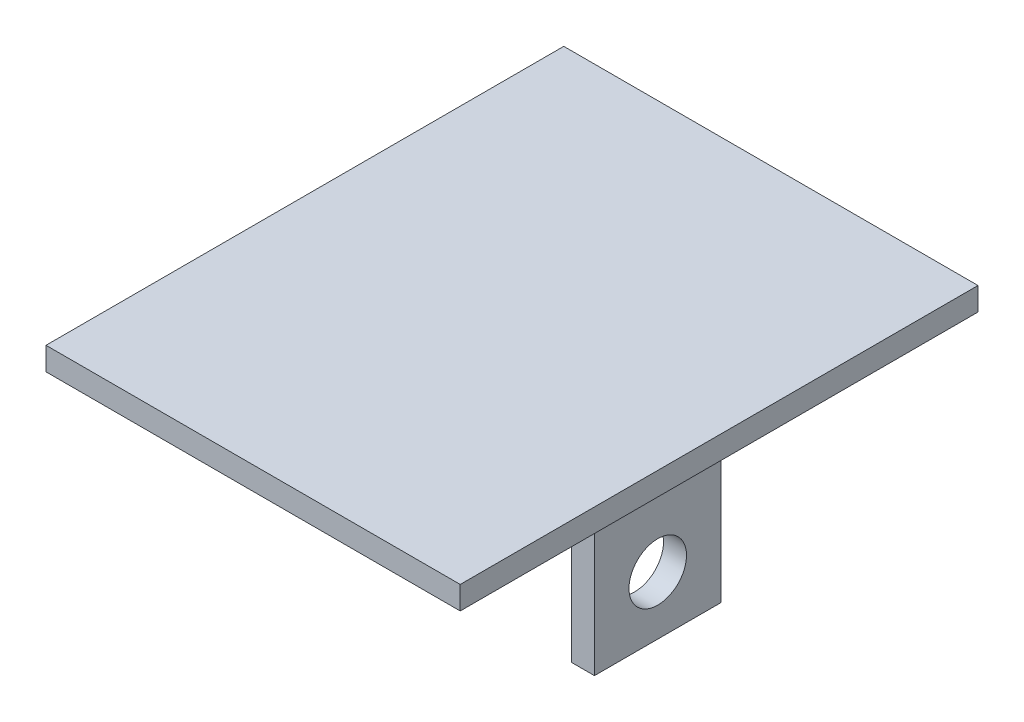
SolidWorks part; units mm, degrees
ref_plane "Alzado" through (0, 0, 0) normal (0, 0, 1) x (1, 0, 0)
ref_plane "Planta" through (0, 0, 0) normal (0, 1, 0) x (1, 0, 0)
ref_plane "Vista lateral" through (0, 0, 0) normal (1, 0, 0) x (0, 0, -1)
sketch "Croquis1" plane through (0, 0, 0) normal (0, 1, 0) x (1, 0, 0)
  line L1 (-18, 22.5) -> (18, 22.5)
  line L2 (-18, 22.5) -> (-18, -22.5)
  line L3 (-18, -22.5) -> (18, -22.5)
  line L4 (18, 22.5) -> (18, -22.5)
  line L5 (-18, 22.5) -> (18, -22.5) construction
  line L6 (-18, -22.5) -> (18, 22.5) construction
  point P0 (0, 0)
extrude "Saliente-Extruir1" add sketch "Croquis1" along normal blind 2
sketch "Croquis2" plane through (0, 2, 0) normal (0, 1, 0) x (1, 0, 0)
  line L0 (18, 0) -> (10.7, 0)
  line L1 (18, -22.5) -> (18, 22.5) construction
  line L2 (-18, 0) -> (-15, 0)
  line L3 (-18, 22.5) -> (-18, -22.5) construction
  line L4 (-15, 0) -> (-15, 5.5)
  line L5 (10.7, 0) -> (10.7, 5.4661)
  line L7 (10.7, 5.4661) -> (12.7, 5.4661)
  line L8 (10.7, 5.4661) -> (10.7, -5.5339)
  line L9 (10.7, -5.5339) -> (12.7, -5.5339)
  line L10 (12.7, 5.4661) -> (12.7, -5.5339)
  line L11 (-15, 5.5) -> (-17, 5.5)
  line L12 (-15, 5.5) -> (-15, -5.5339)
  line L13 (-15, -5.5339) -> (-17, -5.5339)
  line L14 (-17, 5.5) -> (-17, -5.5339)
extrude "Saliente-Extruir2" add sketch "Croquis2" against normal blind 18 contours L11 L14 L13 L12 | L7 L10 L9 L8
sketch "Croquis3" plane through (12.7, 0, 0) normal (1, 0, 0) x (0, 0, -1)
  line L0 (-0.0339, -16) -> (-0.0339, -10.94)
  line L1 (5.4661, -16) -> (-5.5339, -16) construction
  circle A0 centre (-0.0339, -10.94) radius 2.5
extrude "Cortar-Extruir1" cut sketch "Croquis3" against normal blind 33
